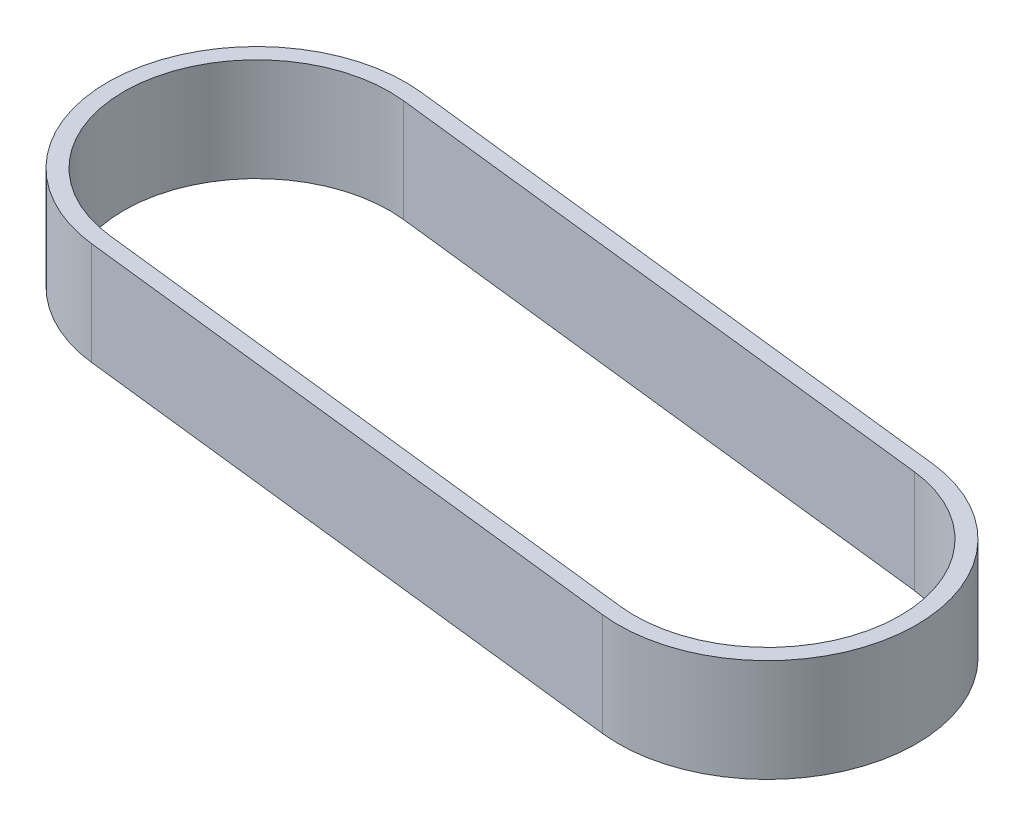
SolidWorks part; units mm, degrees
material "Rubber"
ref_plane "Front Plane" through (0, 0, 0) normal (0, 0, 1) x (1, 0, 0)
ref_plane "Top Plane" through (0, 0, 0) normal (0, 1, 0) x (1, 0, 0)
ref_plane "Right Plane" through (0, 0, 0) normal (1, 0, 0) x (0, 0, -1)
sketch "Sketch1" plane through (0, 0, 0) normal (0, 1, 0) x (1, 0, 0)
  line L0 (0, 0) -> (54.102, -6.1779) construction
  line L1 (1.412, 12.3656) -> (55.514, 6.1877)
  line L2 (-1.412, -12.3656) -> (52.69, -18.5436)
  line L3 (1.5849, 13.8798) -> (55.6869, 7.7019)
  line L4 (-1.5849, -13.8798) -> (52.5171, -20.0577)
  arc A0 (1.412, 12.3656) -> (-1.412, -12.3656) centre (0, 0) ccw
  arc A1 (52.69, -18.5436) -> (55.514, 6.1877) centre (54.102, -6.1779) ccw
  arc A2 (52.5171, -20.0577) -> (55.6869, 7.7019) centre (54.102, -6.1779) ccw
  arc A3 (1.5849, 13.8798) -> (-1.5849, -13.8798) centre (0, 0) ccw
  point P3 (27.051, -3.089)
  dimension "D3" = 12.446
  dimension "D1" = 54.102
  dimension "D2" = 1.524
extrude "Boss-Extrude1" add sketch "Sketch1" along normal blind 9.652
